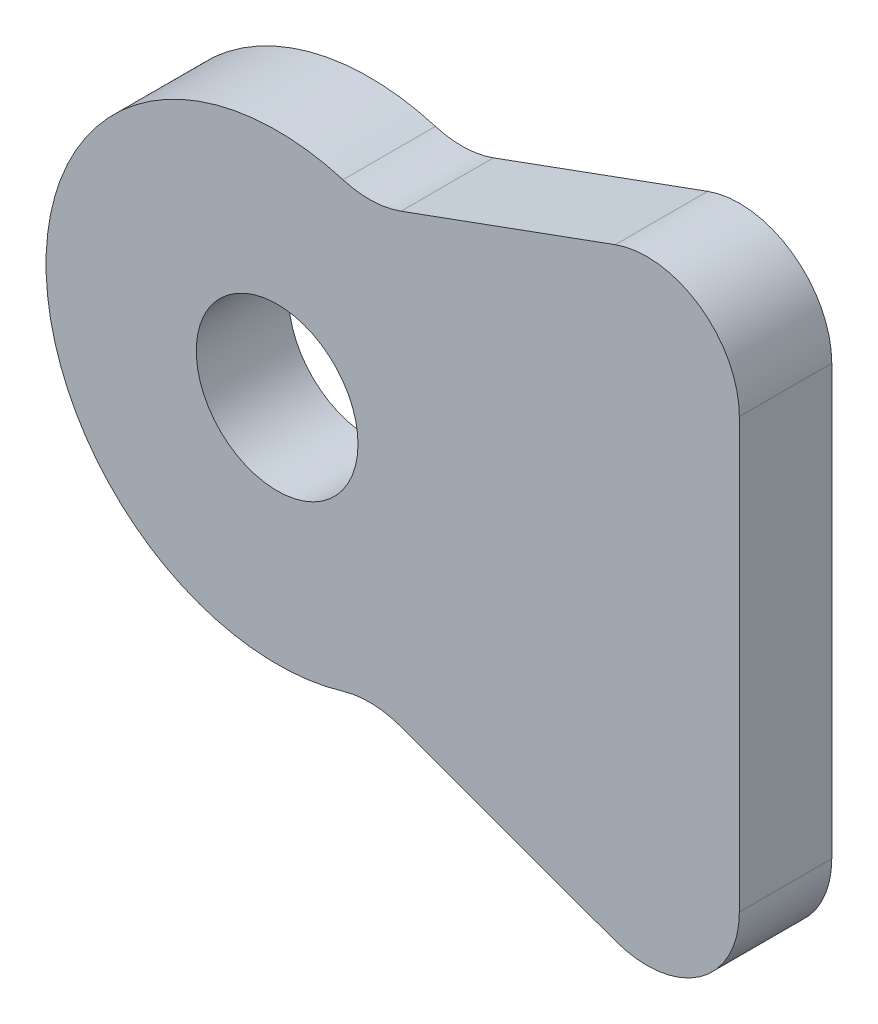
SolidWorks part; units mm, degrees
ref_plane "Front" through (0, 0, 0) normal (0, 0, 1) x (1, 0, 0)
ref_plane "Top" through (0, 0, 0) normal (0, 1, 0) x (1, 0, 0)
ref_plane "Right" through (0, 0, 0) normal (1, 0, 0) x (0, 0, -1)
sketch "Esquisse1" plane through (0, 0, 0) normal (0, 0, 1) x (1, 0, 0)
  circle A0 centre (0, 0) radius 1.75
  circle A1 centre (0, 0) radius 5
  dimension "D1" = 3.5
  dimension "D2" = 10
extrude "Boss.-Extru.1" add sketch "Esquisse1" along normal blind 2
sketch "Esquisse2" plane through (0, 0, 2) normal (0, 0, 1) x (1, 0, 0)
  line L0 (0, 0) -> (10, 0) construction
  line L1 (10, 7.5) -> (10, -7.5)
  line L2 (10, -7.5) -> (2, -4.5826)
  line L3 (2, -4.5826) -> (2, 4.5826)
  line L4 (10, 7.5) -> (2, 4.5826)
  circle A1 centre (0, 0) radius 5 construction
  point P9 (2, 0)
  dimension "D1" = 15
  dimension "D2" = 10
  dimension "D3" = 8
extrude "Boss.-Extru.2" add sketch "Esquisse2" against normal blind 2
fillet "Congé1" radius 2 4 edges at (2, -4.5826, 1) (2, 4.5826, 1) (10, -7.5, 1) (10, 7.5, 1)
